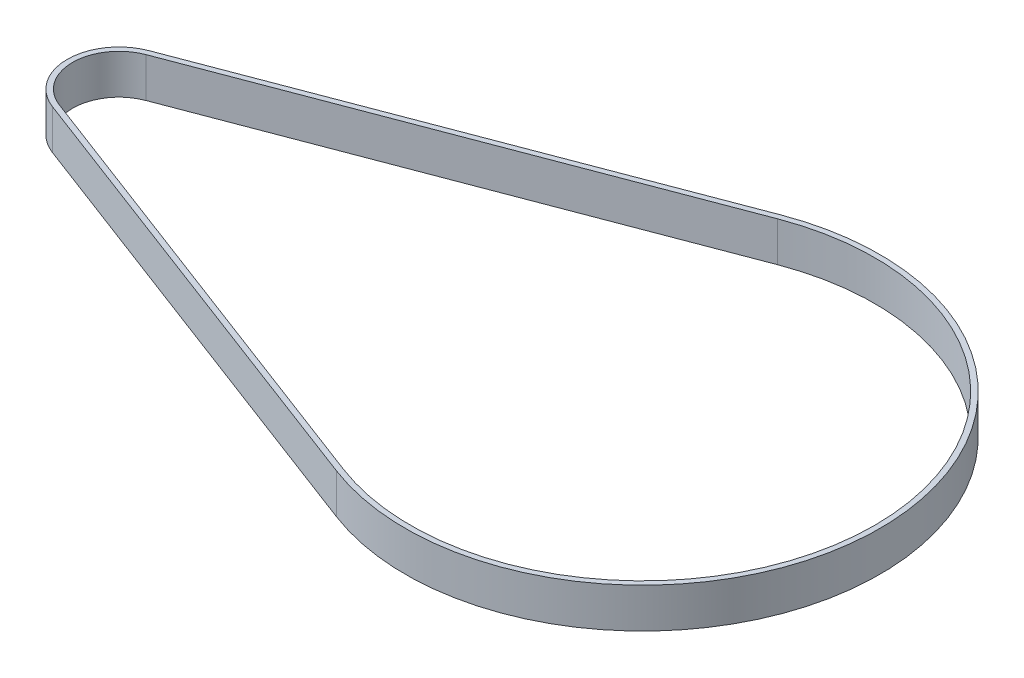
SolidWorks part; units mm, degrees
ref_plane "Front Plane" through (0, 0, 0) normal (0, 0, 1) x (1, 0, 0)
ref_plane "Top Plane" through (0, 0, 0) normal (0, 1, 0) x (1, 0, 0)
ref_plane "Right Plane" through (0, 0, 0) normal (1, 0, 0) x (0, 0, -1)
sketch "Sketch1" plane through (0, 0, 0) normal (0, 1, 0) x (1, 0, 0)
  line L0 (-81.481, 6.5456) -> (-12.4051, 32.7279)
  line L1 (-81.481, -6.5456) -> (-12.4051, -32.7279)
  line L2 (-81.7646, 7.2936) -> (-12.6886, 33.476)
  line L3 (-81.7646, -7.2936) -> (-12.6886, -33.476)
  arc A0 (-12.4051, -32.7279) -> (-12.4051, 32.7279) centre (0, 0) ccw
  arc A1 (-81.481, 6.5456) -> (-81.481, -6.5456) centre (-79, 0) ccw
  arc A2 (-12.6886, -33.476) -> (-12.6886, 33.476) centre (0, 0) ccw
  arc A3 (-81.7646, 7.2936) -> (-81.7646, -7.2936) centre (-79, 0) ccw
  dimension "D1" = 14
  dimension "D2" = 70
  dimension "D3" = 79
  dimension "D4" = 0.8
extrude "Boss-Extrude1" add sketch "Sketch1" along normal blind 6
